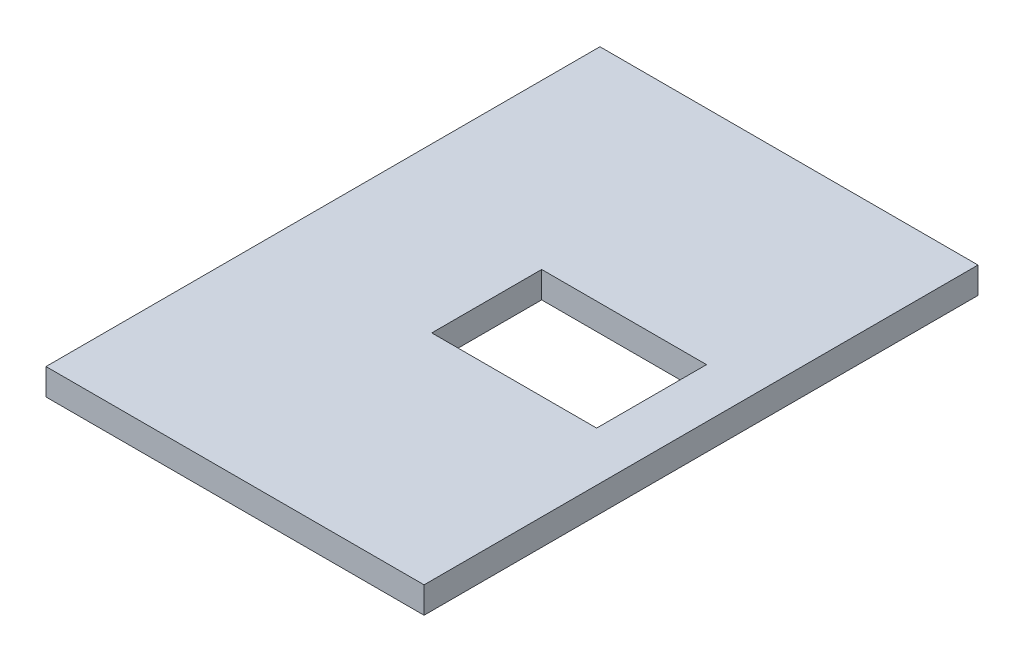
SolidWorks part; units mm, degrees
ref_plane "Alzado" through (0, 0, 0) normal (0, 0, 1) x (1, 0, 0)
ref_plane "Planta" through (0, 0, 0) normal (0, 1, 0) x (1, 0, 0)
ref_plane "Vista lateral" through (0, 0, 0) normal (1, 0, 0) x (0, 0, -1)
sketch "Croquis1" plane through (0, 0, 0) normal (0, 1, 0) x (1, 0, 0)
  line L0 (735, 1260) -> (-885, 1260)
  line L1 (735, 1260) -> (735, -1260)
  line L2 (735, -1260) -> (-885, -1260)
  line L3 (-885, 1260) -> (-885, -1260)
  line L4 (735, 1260) -> (-885, -1260) construction
  line L5 (735, -1260) -> (-885, 1260) construction
  line L6 (735, 0) -> (235, 0) construction
  line L7 (-140, 250) -> (610, 250)
  line L8 (-140, 250) -> (-140, -250)
  line L9 (-140, -250) -> (610, -250)
  line L10 (610, 250) -> (610, -250)
  line L11 (-140, 250) -> (610, -250) construction
  line L12 (-140, -250) -> (610, 250) construction
  point P0 (-75, 0)
  dimension "D1" = 1620
  dimension "D2" = 500
  dimension "D3" = 500
  dimension "D4" = 750
extrude "Saliente-Extruir1" add sketch "Croquis1" along normal blind 120
sketch "Croquis2" plane through (735, 0, 0) normal (1, 0, 0) x (0, 0, -1)
  line L0 (-1260, 120) -> (1260, 120)
  line L1 (1260, 120) -> (1260, 0)
  line L2 (1260, 0) -> (-1260, 0)
  line L3 (-1260, 0) -> (-1260, 120)
extrude "Saliente-Extruir2" add sketch "Croquis2" along normal blind 100
